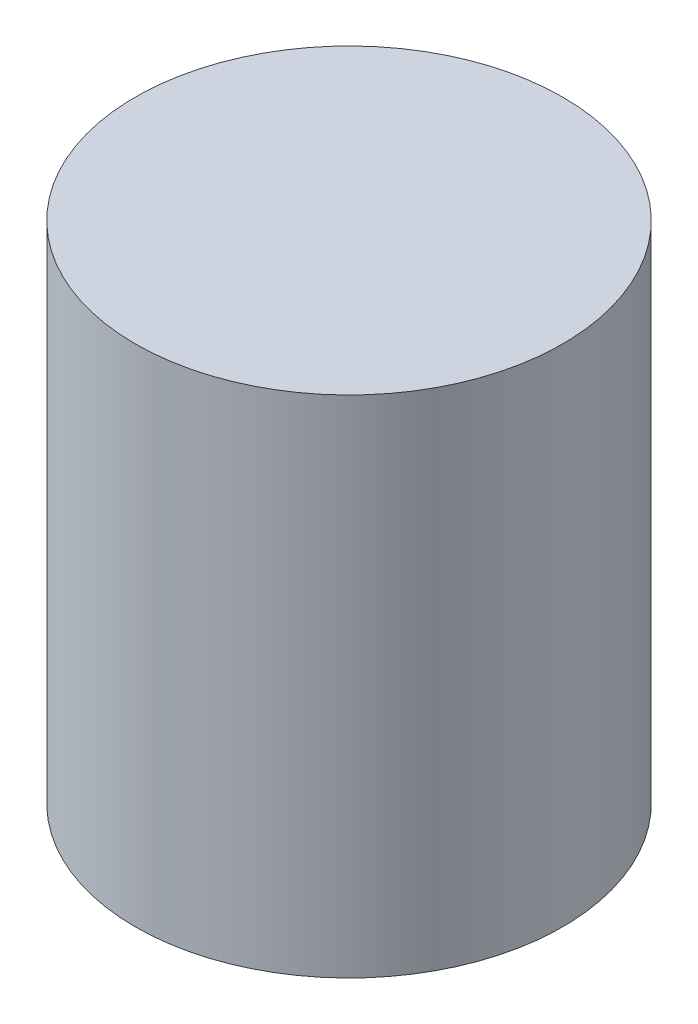
SolidWorks part; units mm, degrees
ref_plane "Front Plane" through (0, 0, 0) normal (0, 0, 1) x (1, 0, 0)
ref_plane "Top Plane" through (0, 0, 0) normal (0, 1, 0) x (1, 0, 0)
ref_plane "Right Plane" through (0, 0, 0) normal (1, 0, 0) x (0, 0, -1)
sketch "Sketch1" plane through (0, 0, 0) normal (0, 1, 0) x (1, 0, 0)
  circle A0 centre (0, 0) radius 12.7
  dimension "D1" = 25.4
extrude "Boss-Extrude1" add sketch "Sketch1" along normal blind 30 contours A0
sketch "Sketch2" plane through (0, 30, 0) normal (0, 1, 0) x (1, 0, 0)
  point P0 (0, 0)
sketch "Sketch3" plane through (0, 0, 0) normal (0, -1, 0) x (1, 0, 0)
  point P0 (0, 0)
